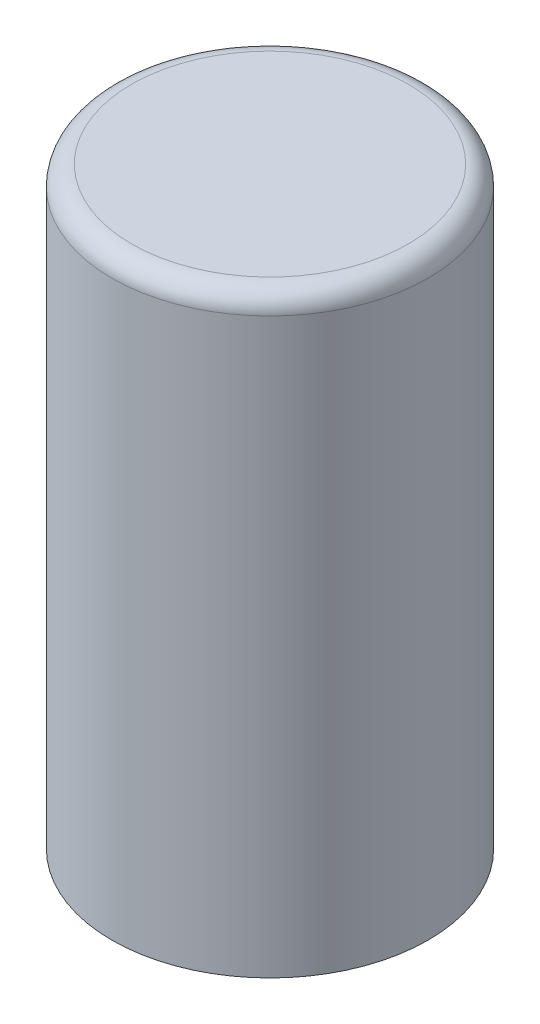
SolidWorks part; units mm, degrees
ref_plane "Front Plane" through (0, 0, 0) normal (0, 0, 1) x (1, 0, 0)
ref_plane "Top Plane" through (0, 0, 0) normal (0, 1, 0) x (1, 0, 0)
ref_plane "Right Plane" through (0, 0, 0) normal (1, 0, 0) x (0, 0, -1)
sketch "Sketch1" plane through (0, 0, 0) normal (0, 1, 0) x (1, 0, 0)
  circle A0 centre (0, 0) radius 4
  dimension "D1" = 8
extrude "Boss-Extrude1" add sketch "Sketch1" along normal blind 15
fillet "Fillet1" radius 0.5 1 edges at (0, 15, 4)
